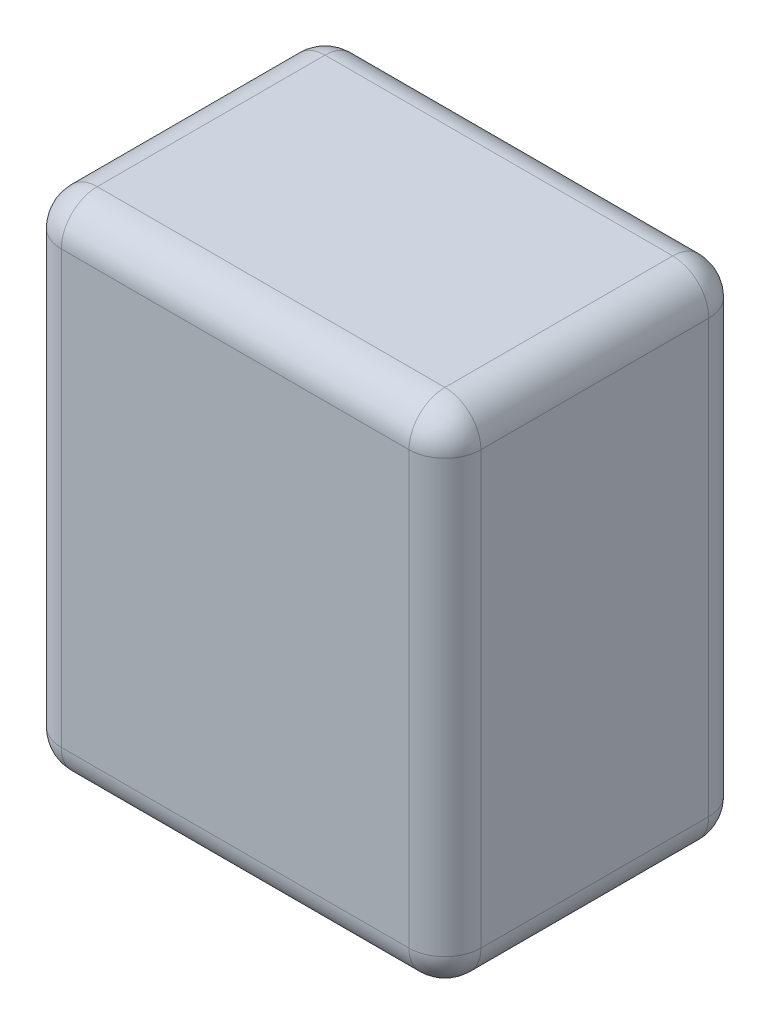
SolidWorks part; units mm, degrees
ref_plane "Front Plane" through (0, 0, 0) normal (0, 0, 1) x (1, 0, 0)
ref_plane "Top Plane" through (0, 0, 0) normal (0, 1, 0) x (1, 0, 0)
ref_plane "Right Plane" through (0, 0, 0) normal (1, 0, 0) x (0, 0, -1)
sketch "Sketch1" plane through (0, 0, 0) normal (0, 1, 0) x (1, 0, 0)
  line L1 (-17.5, 12.5) -> (17.5, 12.5)
  line L2 (-17.5, 12.5) -> (-17.5, -12.5)
  line L3 (-17.5, -12.5) -> (17.5, -12.5)
  line L4 (17.5, 12.5) -> (17.5, -12.5)
  line L5 (-17.5, 12.5) -> (17.5, -12.5) construction
  line L6 (-17.5, -12.5) -> (17.5, 12.5) construction
  point P0 (0, 0)
  dimension "D1" = 25
  dimension "D2" = 35
extrude "Boss-Extrude1" add sketch "Sketch1" along normal blind 42
fillet "Fillet1" radius 3 12 edges at (17.5, 21, -12.5) (-17.5, 21, -12.5) (-17.5, 21, 12.5) (17.5, 21, 12.5) (0, 42, 12.5) (-17.5, 42, 0) (0, 42, -12.5) (17.5, 42, 0) (0, 0, 12.5) (-17.5, 0, 0) (0, 0, -12.5) (17.5, 0, 0)
